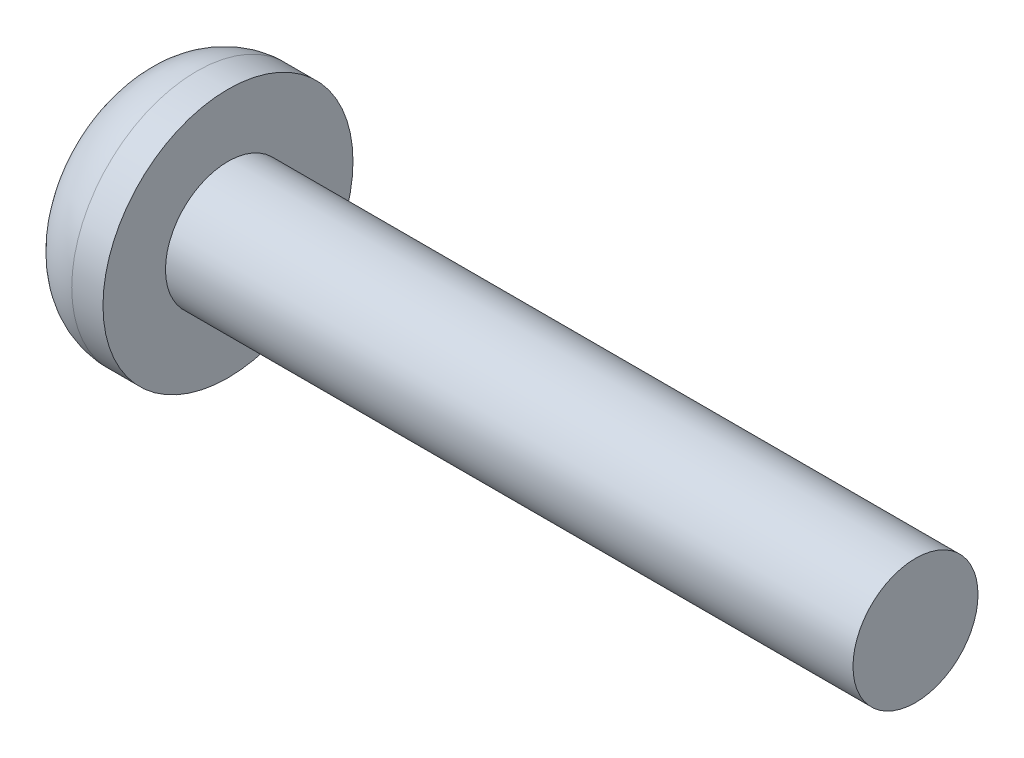
SolidWorks part; units mm, degrees
ref_plane "Front Plane" through (0, 0, 0) normal (0, 0, 1) x (1, 0, 0)
ref_plane "Top Plane" through (0, 0, 0) normal (0, 1, 0) x (1, 0, 0)
ref_plane "Right Plane" through (0, 0, 0) normal (1, 0, 0) x (0, 0, -1)
sketch "Sketch1" plane through (0, 0, 0) normal (1, 0, 0) x (0, 0, -1)
  circle A0 centre (0, 0) radius 1
extrude "Boss-Extrude1" add sketch "Sketch1" along normal blind 11
sketch "Sketch2" plane through (0, 0, 0) normal (-1, 0, 0) x (0, 0, 1)
  circle A0 centre (0, 0) radius 2
extrude "Boss-Extrude2" add sketch "Sketch2" along normal blind 1.5
fillet "Fillet1" radius 1 1 edges at (-1.5, 0, 2)
